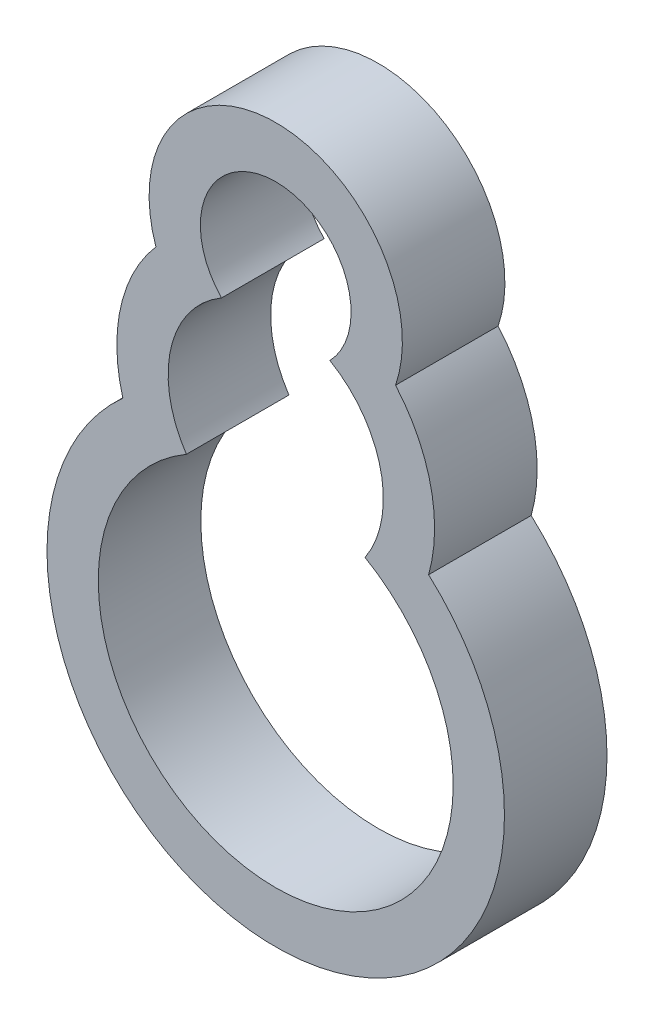
SolidWorks part; units mm, degrees
ref_plane "Front Plane" through (0, 0, 0) normal (0, 0, 1) x (1, 0, 0)
ref_plane "Top Plane" through (0, 0, 0) normal (0, 1, 0) x (1, 0, 0)
ref_plane "Right Plane" through (0, 0, 0) normal (1, 0, 0) x (0, 0, -1)
sketch "Sketch1" plane through (0, 0, 0) normal (0, 0, 1) x (1, 0, 0)
  arc A0 (5.2836, 18.0862) -> (-5.2836, 18.0862) centre (0, 23.1953) ccw
  arc A1 (-5.2836, 18.0862) -> (-8.711, 3.1703) centre (0, 9.0204) ccw
  arc A2 (-8.711, 3.1703) -> (8.711, 3.1703) centre (0, -11.7817) ccw
  arc A3 (8.711, 3.1703) -> (5.2836, 18.0862) centre (0, 9.0204) ccw
  arc A4 (11.6839, 19.195) -> (-11.6839, 19.195) centre (0, 23.1953) ccw
  arc A5 (-11.6839, 19.195) -> (-14.9093, 4.8074) centre (0, 9.0204) ccw
  arc A6 (-14.9093, 4.8074) -> (14.9093, 4.8074) centre (0, -11.7817) ccw
  arc A7 (14.9093, 4.8074) -> (11.6839, 19.195) centre (0, 9.0204) ccw
  dimension "D1" = 5
extrude "Boss-Extrude1" add sketch "Sketch1" along normal blind 10
